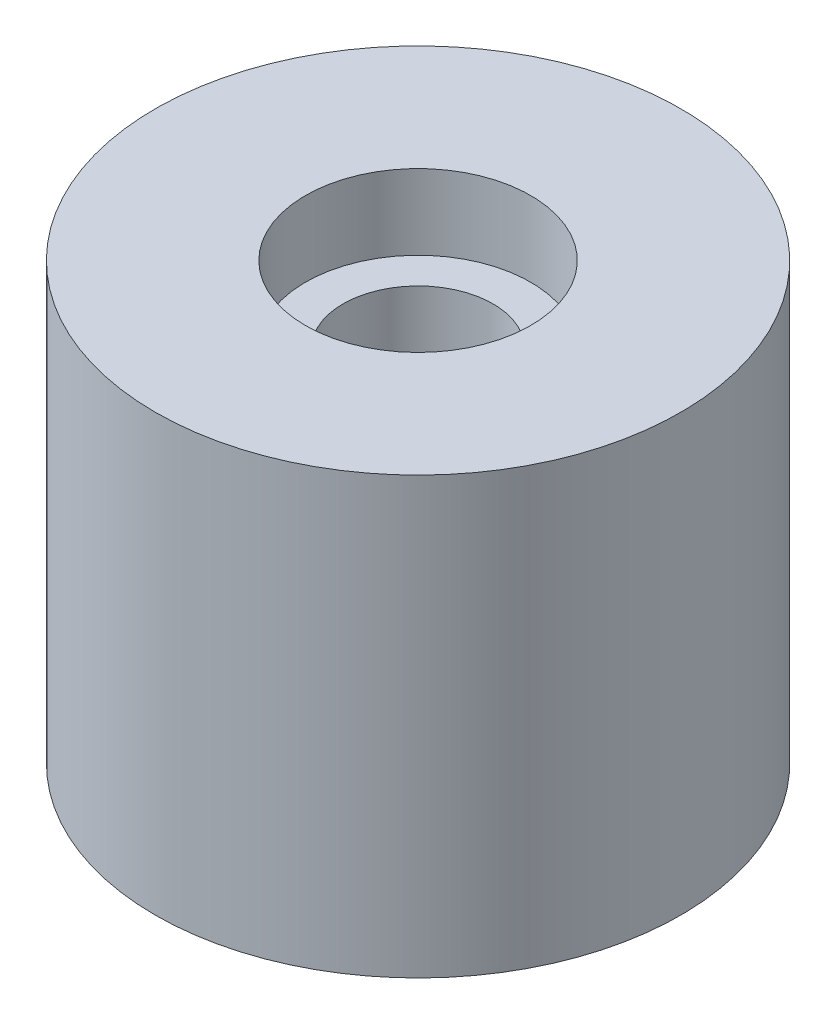
SolidWorks part; units mm, degrees
ref_plane "Front Plane" through (0, 0, 0) normal (0, 0, 1) x (1, 0, 0)
ref_plane "Top Plane" through (0, 0, 0) normal (0, 1, 0) x (1, 0, 0)
ref_plane "Right Plane" through (0, 0, 0) normal (1, 0, 0) x (0, 0, -1)
sketch "Sketch1" plane through (0, 0, 0) normal (0, 0, 1) x (1, 0, 0)
  line L0 (0, 16.0475) -> (0, -13.9525) construction
  line L1 (7.5, 15.0475) -> (7.5, 10.0475)
  line L2 (7.5, -13.9525) -> (17.5, -13.9525)
  line L3 (17.5, -13.9525) -> (17.5, 15.0475)
  line L4 (17.5, 15.0475) -> (7.5, 15.0475)
  line L5 (7.5, 10.0475) -> (5, 10.0475)
  line L6 (5, 10.0475) -> (5, -8.9525)
  line L7 (5, -8.9525) -> (7.5, -8.9525)
  line L8 (7.5, -8.9525) -> (7.5, -13.9525)
  dimension "D1" = 30
  dimension "D2" = 10
  dimension "D3" = 10
  dimension "D4" = 5
  dimension "D5" = 7.5
revolve "Revolve1" add sketch "Sketch1" angle 360 about L0
